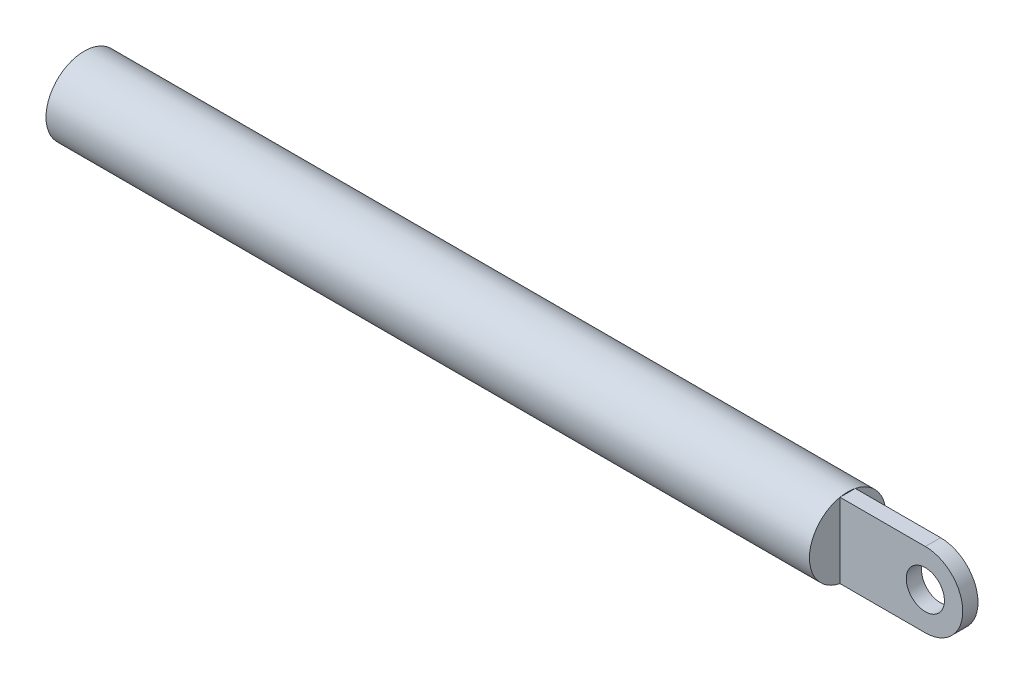
SolidWorks part; units mm, degrees
ref_plane "Спереди" through (0, 0, 0) normal (0, 0, 1) x (1, 0, 0)
ref_plane "Сверху" through (0, 0, 0) normal (0, 1, 0) x (1, 0, 0)
ref_plane "Справа" through (0, 0, 0) normal (1, 0, 0) x (0, 0, -1)
other "Configuration Table"
sketch "Sketch1" plane through (0, 0, 0) normal (0, 0, 1) x (1, 0, 0)
  line L1 (-73.8487, 18.8322) -> (26.1513, 18.8322)
  line L2 (-73.8487, 18.8322) -> (-73.8487, 13.8322)
  line L3 (-73.8487, 13.8322) -> (26.1513, 13.8322)
  line L4 (26.1513, 18.8322) -> (26.1513, 13.8322)
  line L5 (-73.8487, 18.8322) -> (26.1513, 13.8322) construction
  line L6 (-73.8487, 13.8322) -> (26.1513, 18.8322) construction
  point P0 (-23.8487, 16.3322)
  dimension "D1" = 100
  dimension "D2" = 5
revolve "Revolve1" add sketch "Sketch1" angle 360 about L3
sketch "Sketch4" plane through (26.1513, 0, 0) normal (1, 0, 0) x (0, 0, -1)
  line L0 (0, 18.8322) -> (0, 13.8322) construction
  line L1 (-1, 8.9333) -> (1, 8.9333)
  line L2 (-1, 8.9333) -> (-1, 18.7312)
  line L3 (-1, 18.7312) -> (1, 18.7312)
  line L4 (1, 8.9333) -> (1, 18.7312)
  line L5 (-1, 8.9333) -> (1, 18.7312) construction
  line L6 (-1, 18.7312) -> (1, 8.9333) construction
  line L7 (0, 18.8322) -> (0, 13.8322) construction
  circle A0 centre (0, 13.8322) radius 5 construction
  arc A1 (-1, 18.7312) -> (1, 18.7312) centre (0, 13.8322) cw
  arc A2 (-1, 8.9333) -> (1, 8.9333) centre (0, 13.8322) ccw
  point P0 (0, 13.8322)
  dimension "D1" = 2
  dimension "D2" = 2
extrude "Boss-Extrude4" add sketch "Sketch4" along normal blind 20 contours L1 L4 L3 L2
sketch "Sketch10" plane through (0, 0, 1) normal (0, 0, 1) x (1, 0, 0)
  line L0 (46.1513, 18.7312) -> (26.1513, 18.7312) construction
  line L1 (46.1513, 8.9333) -> (26.1513, 8.9333) construction
  line L2 (37.3271, 18.7312) -> (46.1513, 18.7312)
  line L3 (46.1513, 18.7312) -> (46.1513, 8.9333)
  line L4 (46.1513, 8.9333) -> (37.3271, 8.9333)
  arc A0 (37.3271, 18.7312) -> (37.3271, 8.9333) centre (37.3271, 13.8322) cw
extrude "Cut-Extrude5" cut sketch "Sketch10" against normal up to surface (2 mm away) up to face at (36.1513, 13.8322, -1)
sketch "Sketch11" plane through (0, 0, 1) normal (0, 0, 1) x (1, 0, 0)
  circle A0 centre (37.3271, 13.8322) radius 2.5
  dimension "D1" = 5
extrude "Cut-Extrude6" cut sketch "Sketch11" against normal up to surface (2 mm away) up to face at (32.964, 13.8322, -1)
